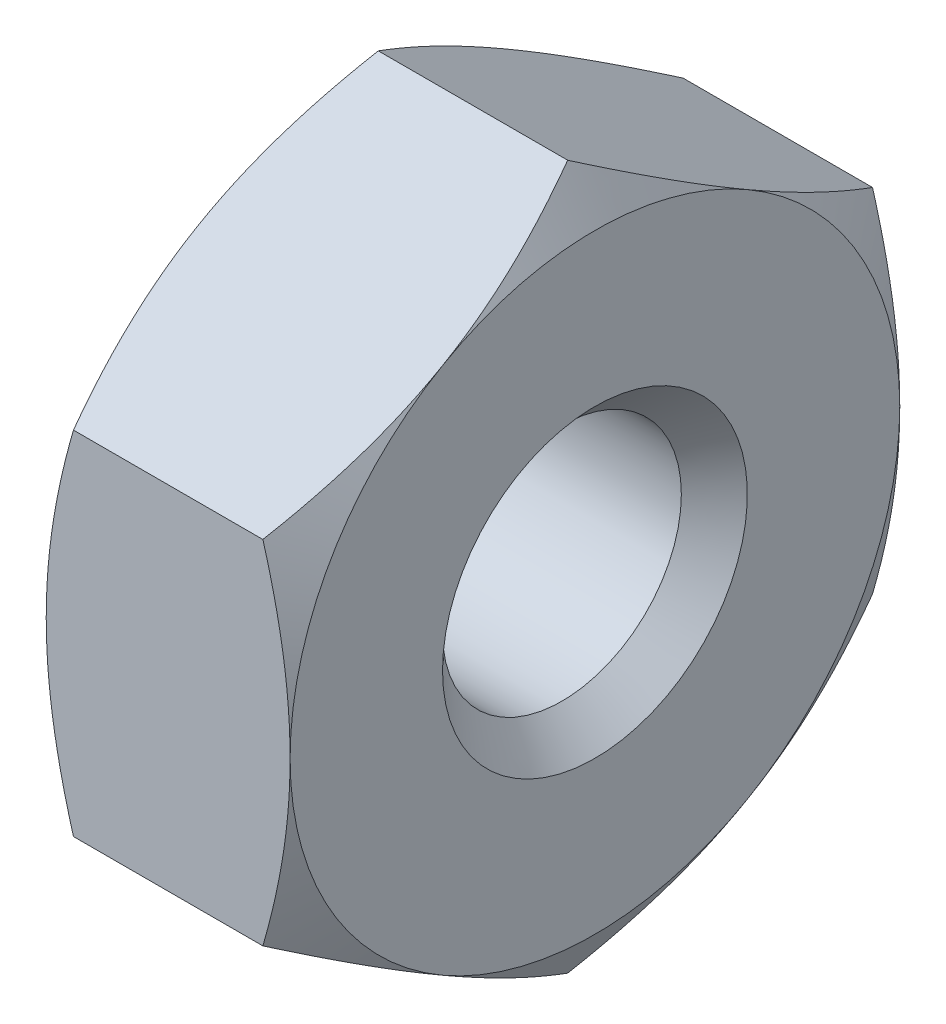
SolidWorks part; units mm, degrees
material "AISI 304"
ref_plane "正面" through (0, 0, 0) normal (0, 0, 1) x (1, 0, 0)
ref_plane "平面" through (0, 0, 0) normal (0, 1, 0) x (1, 0, 0)
ref_plane "右側面" through (0, 0, 0) normal (1, 0, 0) x (0, 0, -1)
ref_plane "Plane1" through (0, 0, 0) normal (0, 0, 1) x (1, 0, 0)
sketch "Sketch1" plane through (0, 0, 0) normal (0, 0, 1) x (1, 0, 0)
  line L0 (0, 0) -> (0, 2)
  line L1 (0, 2) -> (0.2309, 2.4)
  line L2 (0.2309, 2.4) -> (1.3691, 2.4)
  line L3 (1.3691, 2.4) -> (1.6, 2)
  line L4 (1.6, 2) -> (1.6, 0)
  line L5 (1.6, 0) -> (0, 0)
  line L6 (1.6, 0) -> (0, 0) construction
revolve "Revolve1" add sketch "Sketch1" angle 360 about L6
ref_plane "Plane2" through (0, 0, 0) normal (1, 0, 0) x (0, 0, -1)
sketch "Sketch2" plane through (0, 0, 0) normal (1, 0, 0) x (0, 0, -1)
  line L0 (-3, 3) -> (-3, -3)
  line L1 (-3, -3) -> (3, -3)
  line L2 (3, -3) -> (3, 3)
  line L3 (3, 3) -> (-3, 3)
  line L4 (-2, -1.1547) -> (0, -2.3094)
  line L5 (0, -2.3094) -> (2, -1.1547)
  line L6 (2, -1.1547) -> (2, 1.1547)
  line L7 (2, 1.1547) -> (0, 2.3094)
  line L8 (0, 2.3094) -> (-2, 1.1547)
  line L9 (-2, 1.1547) -> (-2, -1.1547)
extrude "Cut-Extrude1" cut sketch "Sketch2" along normal blind 1.6
ref_plane "Plane3" through (0, 0, 0) normal (0, 0, 1) x (1, 0, 0)
sketch "Sketch3" plane through (0, 0, 0) normal (0, 0, 1) x (1, 0, 0)
  line L0 (0, 0) -> (0, 1)
  line L1 (0, 1) -> (0.2165, 0.7835)
  line L2 (0.2165, 0.7835) -> (1.3835, 0.7835)
  line L3 (1.3835, 0.7835) -> (1.6, 1)
  line L4 (1.6, 1) -> (1.6, 0)
  line L5 (1.6, 0) -> (0, 0)
  line L6 (1.6, 0) -> (0, 0) construction
revolve "Cut-Revolve1" cut sketch "Sketch3" angle 360 about L6
